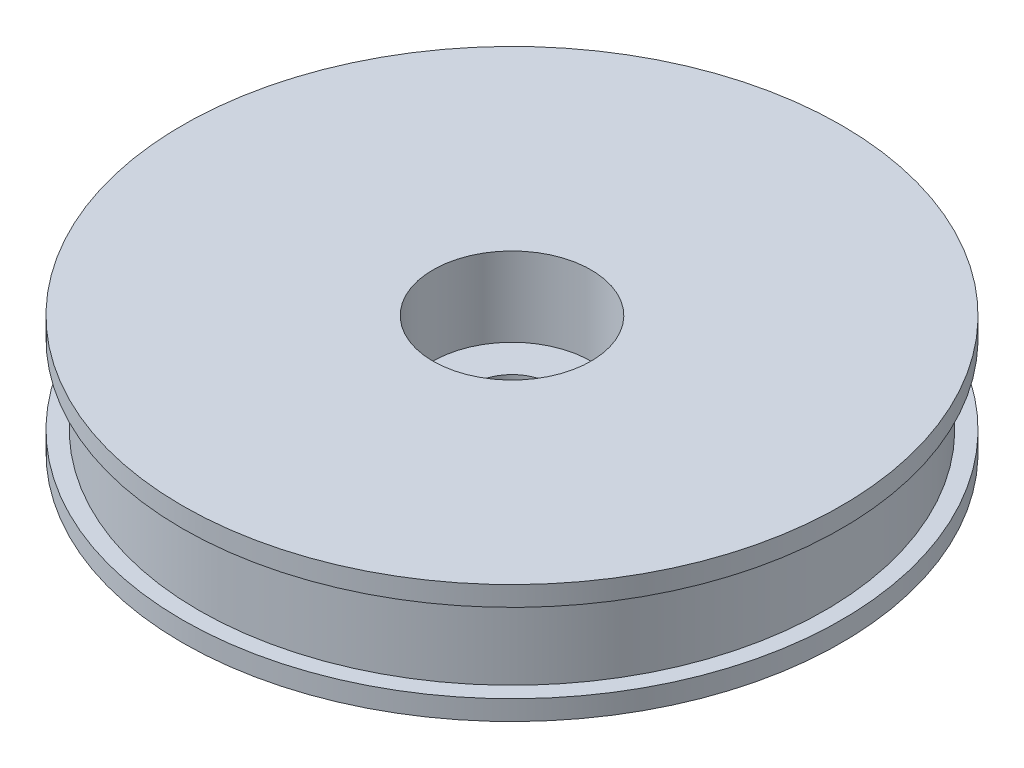
SolidWorks part; units mm, degrees
ref_plane "Front Plane" through (0, 0, 0) normal (0, 0, 1) x (1, 0, 0)
ref_plane "Top Plane" through (0, 0, 0) normal (0, 1, 0) x (1, 0, 0)
ref_plane "Right Plane" through (0, 0, 0) normal (1, 0, 0) x (0, 0, -1)
sketch "Sketch1" plane through (0, 0, 0) normal (0, 1, 0) x (1, 0, 0)
  circle A0 centre (0, 0) radius 12.7
  dimension "D1" = 25.4
extrude "Boss-Extrude1" add sketch "Sketch1" along normal blind 0.762
sketch "Sketch2" plane through (0, 0.762, 0) normal (0, 1, 0) x (1, 0, 0)
  circle A0 centre (0, 0) radius 12.065
  dimension "D1" = 24.13
extrude "Boss-Extrude2" add sketch "Sketch2" along normal blind 3.048
sketch "Sketch3" plane through (0, 3.81, 0) normal (0, 1, 0) x (1, 0, 0)
  circle A0 centre (0, 0) radius 12.7
  dimension "D1" = 25.4
extrude "Boss-Extrude3" add sketch "Sketch3" along normal blind 0.762
sketch "Sketch4" plane through (0, 4.572, 0) normal (0, 1, 0) x (1, 0, 0)
  circle A0 centre (0, 0) radius 3.048
  dimension "D1" = 6.096
extrude "Cut-Extrude1" cut sketch "Sketch4" against normal blind 3.048
sketch "Sketch5" plane through (0, 1.524, 0) normal (0, 1, 0) x (1, 0, 0)
  circle A0 centre (0, 0) radius 1.524
  dimension "D1" = 3.048
extrude "Cut-Extrude2" cut sketch "Sketch5" against normal through all
